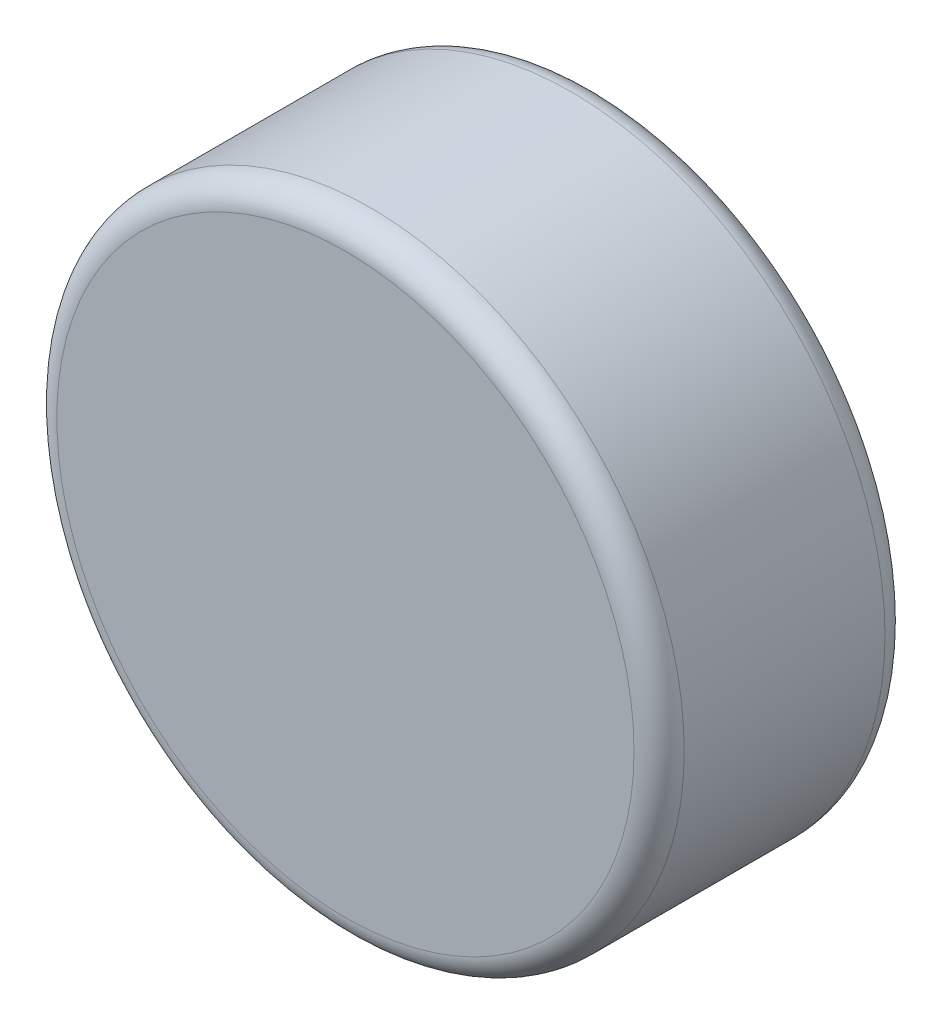
SolidWorks part; units mm, degrees
ref_plane "Front Plane" through (0, 0, 0) normal (0, 0, 1) x (1, 0, 0)
ref_plane "Top Plane" through (0, 0, 0) normal (0, 1, 0) x (1, 0, 0)
ref_plane "Right Plane" through (0, 0, 0) normal (1, 0, 0) x (0, 0, -1)
sketch "Sketch1" plane through (0, 0, 0) normal (0, 0, 1) x (1, 0, 0)
  circle A0 centre (0, 0) radius 2.5
  dimension "D1" = 5
extrude "Boss-Extrude1" add sketch "Sketch1" along normal blind 2
fillet "Fillet1" radius 0.2 2 edges at (2.5, 0, 2) (2.5, 0, 0)
